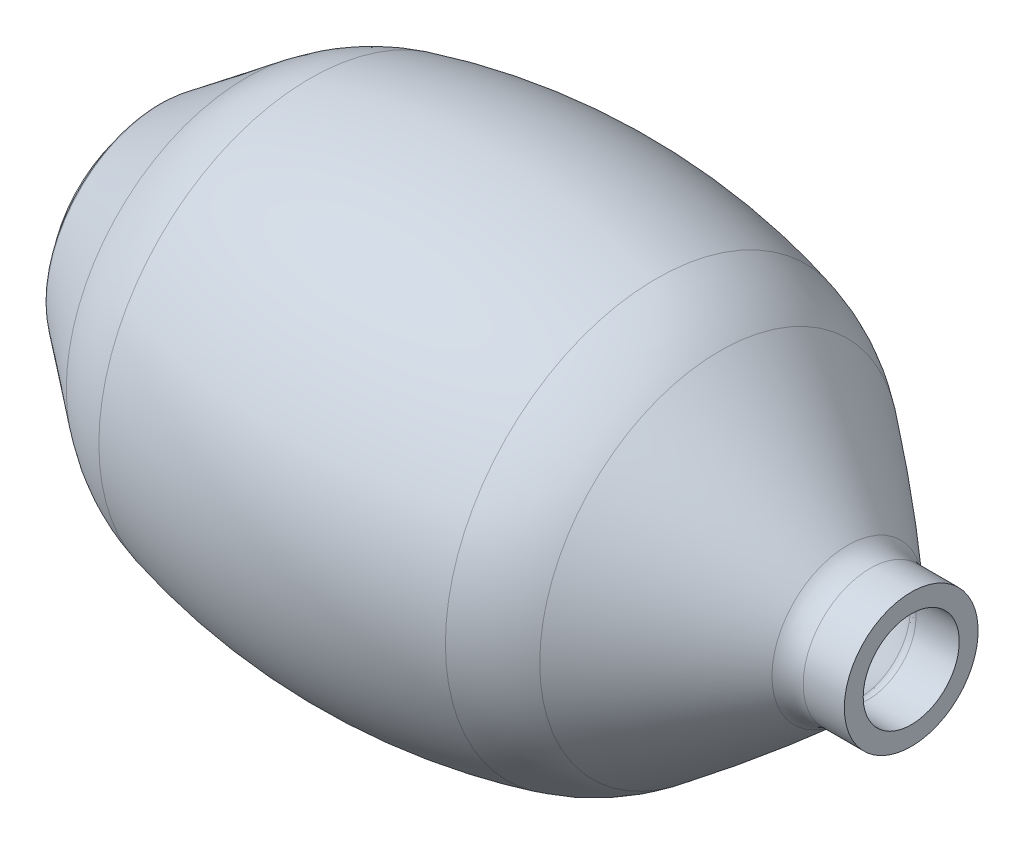
SolidWorks part; units mm, degrees
ref_plane "Front" through (0, 0, 0) normal (0, 0, 1) x (1, 0, 0)
ref_plane "Top" through (0, 0, 0) normal (0, 1, 0) x (1, 0, 0)
ref_plane "Right" through (0, 0, 0) normal (1, 0, 0) x (0, 0, -1)
sketch "Sketch1" plane through (0, 0, 0) normal (0, 1, 0) x (1, 0, 0)
  line L0 (50.5, 61.5) -> (50.5, 0) construction
  line L1 (-50.5, 61.5) -> (-50.5, 0) construction
  line L2 (0, 0) -> (0, 113.5522) construction
  line L3 (0, 0) -> (236.0288, 0) construction
  line L4 (0, 67.9504) -> (133.3657, 67.9504) construction
  line L5 (69, 0) -> (69, 52.5) construction
  line L6 (-69, 0) -> (-69, 52.5) construction
  line L7 (-69, 52.5) -> (-93.6538, 33.7007)
  line L8 (-95.2284, 28) -> (-95.2284, 32.5) construction
  line L9 (-95.2284, 30.5199) -> (-95.2284, 28)
  line L10 (109, 0) -> (109, 19.5) construction
  line L11 (112.7945, 19.5) -> (124.7716, 19.5)
  line L12 (124.7716, 19.5) -> (124.7716, 14)
  line L14 (-95.2284, 28) -> (-98.2284, 28)
  line L15 (-98.2284, 28) -> (-98.2284, 25.5)
  line L16 (-98.2284, 25.5) -> (-92.2284, 25.5)
  line L17 (112.1726, 14) -> (124.7716, 14)
  line L20 (-95.2284, 30.5199) -> (-95.2284, 25.5) construction
  line L21 (-65.665, 48.1264) -> (-89.7284, 29.7774) construction
  line L22 (-89.7284, 29.7774) -> (-89.7284, 25.5) construction
  line L23 (-67.1809, 50.1144) -> (-91.8348, 31.3151)
  line L24 (112.7945, 14) -> (124.7716, 14) construction
  line L29 (-92.2284, 30.5199) -> (-92.2284, 25.5)
  line L30 (-67.1809, 50.1144) -> (-91.8348, 31.3151) construction
  line L31 (-69, 52.5) -> (-93.6538, 33.7007) construction
  arc A0 (50.5, 61.5) -> (-50.5, 61.5) centre (0, -132.9579) ccw
  arc A1 (69, 52.5) -> (50.5, 61.5) centre (37.401, 11.0605) ccw
  arc A2 (-69, 52.5) -> (-50.5, 61.5) centre (-37.401, 11.0605) cw
  arc A3 (106.1814, 21.9988) -> (69, 52.5) centre (-341.2986, -485.574) ccw
  arc A4 (112.7945, 19.5) -> (106.1814, 21.9988) centre (112.7945, 29.5) cw
  arc A12 (112.7945, 14) -> (102.5442, 17.8732) centre (112.7945, 29.5) cw construction
  arc A13 (-65.665, 48.1264) -> (-49.1175, 56.1766) centre (-37.401, 11.0605) cw construction
  arc A14 (49.1175, 56.1766) -> (-49.1175, 56.1766) centre (0, -132.9579) ccw construction
  arc A15 (65.665, 48.1264) -> (49.1175, 56.1766) centre (37.401, 11.0605) ccw construction
  arc A16 (102.5442, 17.8732) -> (65.665, 48.1264) centre (-341.2986, -485.574) ccw construction
  arc A17 (65.9416, 52.2517) -> (52.1925, 58.9404) centre (37.401, 11.0605) ccw
  arc A18 (-65.9416, 52.2517) -> (-52.1925, 58.9404) centre (-37.401, 11.0605) cw
  arc A19 (49.7459, 58.5963) -> (-49.7459, 58.5963) centre (0, -132.9579) ccw
  arc A20 (109.4959, 15.0276) -> (67.1809, 50.1144) centre (-341.2986, -485.574) ccw
  arc A21 (104.1975, 19.7485) -> (67.1809, 50.1144) centre (-341.2986, -485.574) ccw construction
  arc A22 (112.1726, 14) -> (109.4959, 15.0276) centre (112.1726, 18) cw
  arc A23 (49.7459, 58.5963) -> (50.5322, 58.7193) centre (49.9973, 59.5642) ccw
  arc A24 (66.7924, 50.809) -> (67.1809, 50.1144) centre (67.7873, 50.9096) ccw
  arc A25 (65.9416, 52.2517) -> (66.7924, 50.809) centre (64.8025, 50.6077) cw
  arc A26 (67.7873, 50.9096) -> (49.9973, 59.5642) centre (37.401, 11.0605) ccw construction
  arc A27 (50.5322, 58.7193) -> (52.1925, 58.9404) centre (51.6021, 57.0296) cw
  arc A28 (-50.5322, 58.7193) -> (-49.7459, 58.5963) centre (-49.9973, 59.5642) ccw
  arc A29 (-67.1809, 50.1144) -> (-66.7924, 50.809) centre (-67.7873, 50.9096) ccw
  arc A30 (-67.7873, 50.9096) -> (-49.9973, 59.5642) centre (-37.401, 11.0605) cw construction
  arc A31 (-66.7924, 50.809) -> (-65.9416, 52.2517) centre (-64.8025, 50.6077) cw
  arc A32 (-52.1925, 58.9404) -> (-50.5322, 58.7193) centre (-51.6021, 57.0296) cw
  arc A34 (-92.2284, 30.5199) -> (-91.8348, 31.3151) centre (-91.2284, 30.5199) cw
  arc A35 (-95.2284, 30.5199) -> (-93.6538, 33.7007) centre (-91.2284, 30.5199) cw construction
  arc A36 (-95.2284, 30.5199) -> (-93.6538, 33.7007) centre (-91.2284, 30.5199) cw
  arc A37 (-89.7284, 29.7774) -> (-89.7284, 29.7774) centre (-89.7284, 29.7774) cw construction
  dimension "D5" = 105
  dimension "D10" = 10
  dimension "D11" = 4
  dimension "D21" = 4
  dimension "D22" = 2
  dimension "D23" = 2
  dimension "D24" = 2
  dimension "D25" = 1
  dimension "D1" = 123
  dimension "D2" = 135.9007
  dimension "D3" = 101
  dimension "D4" = 138
  dimension "D6" = 65
  dimension "D7" = 39
  dimension "D8" = 40
  dimension "D9" = 220
  dimension "D12" = 56
  dimension "D13" = 2.5
  dimension "D14" = 3
  dimension "D16" = 2
  dimension "D15" = 28
  dimension "D17" = 2
  dimension "D18" = 3
  dimension "D19" = 3
  dimension "D20" = 3
revolve "Revolve1" add sketch "Sketch1" angle 360 about L3
